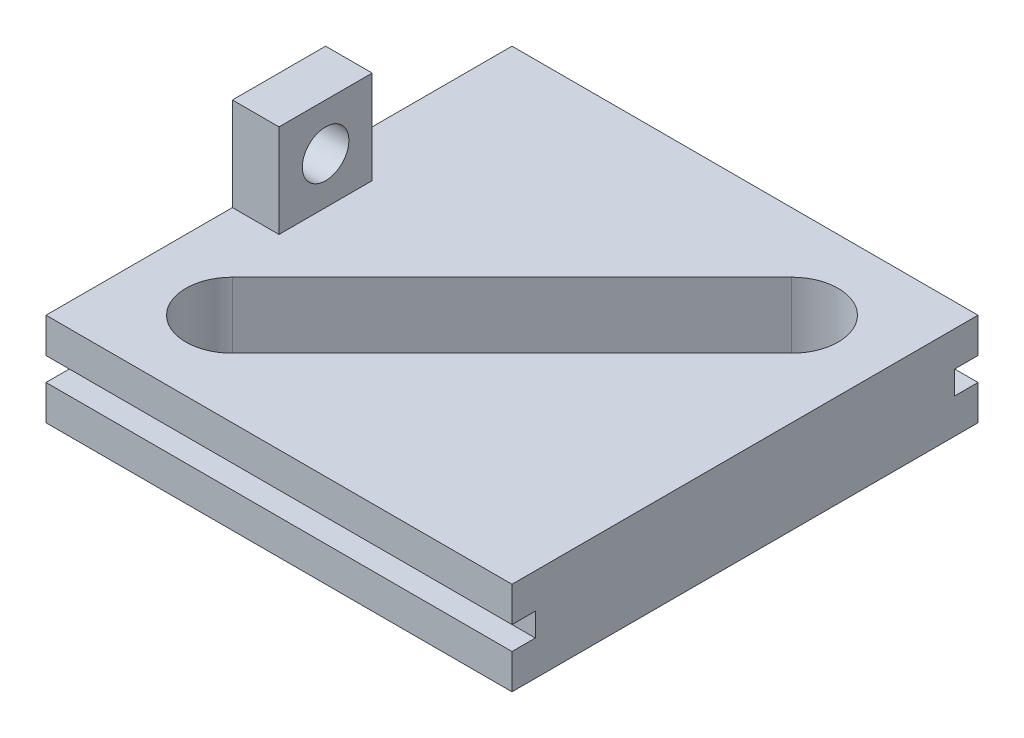
SolidWorks part; units mm, degrees
ref_plane "Front Plane" through (0, 0, 0) normal (0, 0, 1) x (1, 0, 0)
ref_plane "Top Plane" through (0, 0, 0) normal (0, 1, 0) x (1, 0, 0)
ref_plane "Right Plane" through (0, 0, 0) normal (1, 0, 0) x (0, 0, -1)
sketch "Sketch1" plane through (0, 0, 0) normal (0, 1, 0) x (1, 0, 0)
  line L0 (-23.5401, -14.5599) -> (14.5599, 23.5401)
  line L1 (31.75, 31.75) -> (-31.75, 31.75)
  line L2 (31.75, 31.75) -> (31.75, -31.75)
  line L3 (31.75, -31.75) -> (-31.75, -31.75)
  line L4 (-31.75, 31.75) -> (-31.75, -31.75)
  line L5 (31.75, 31.75) -> (-31.75, -31.75) construction
  line L6 (31.75, -31.75) -> (-31.75, 31.75) construction
  line L7 (-14.5599, -23.5401) -> (23.5401, 14.5599)
  line L8 (2.9653, 11.9455) -> (11.9455, 2.9653) construction
  line L9 (14.5599, 23.5401) -> (23.5401, 14.5599) construction
  line L10 (-19.05, -19.05) -> (19.05, 19.05) construction
  arc A0 (-23.5401, -14.5599) -> (-14.5599, -23.5401) centre (-19.05, -19.05) ccw
  arc A1 (14.5599, 23.5401) -> (23.5401, 14.5599) centre (19.05, 19.05) cw
  point P0 (0, 0)
  point P14 (7.4554, 7.4554)
  point P15 (0, 0)
  dimension "D1" = 63.5
  dimension "D2" = 38.1
  dimension "D3" = 12.7
extrude "Boss-Extrude1" add sketch "Sketch1" along normal blind 12.7
sketch "Sketch2" plane through (0, 0, 31.75) normal (0, 0, 1) x (1, 0, 0)
  line L0 (-31.75, 12.7) -> (-31.75, 0) construction
  line L1 (-31.75, 7.9375) -> (31.75, 7.9375)
  line L2 (-31.75, 7.9375) -> (-31.75, 4.7625)
  line L3 (-31.75, 4.7625) -> (31.75, 4.7625)
  line L4 (31.75, 7.9375) -> (31.75, 4.7625)
  line L5 (31.75, 12.7) -> (31.75, 0) construction
  line L6 (13.2782, 12.7) -> (13.2782, 0) construction
  line L7 (-31.75, 12.7) -> (31.75, 12.7) construction
  line L8 (-31.75, 0) -> (31.75, 0) construction
  point P14 (31.75, 6.35)
  point P15 (13.2782, 6.35)
  dimension "D1" = 3.175
extrude "Cut-Extrude1" cut sketch "Sketch2" against normal blind 3.175
mirror "Mirror1" about plane through (0, 0, 0) normal (0, 0, 1) of "Cut-Extrude1"
sketch "Sketch3" plane through (0, 12.7, 0) normal (0, 1, 0) x (1, 0, 0)
  line L0 (-31.75, 31.75) -> (-31.75, -31.75) construction
  line L1 (-31.75, 6.35) -> (-25.4, 6.35)
  line L2 (-31.75, 6.35) -> (-31.75, -6.35)
  line L3 (-31.75, -6.35) -> (-25.4, -6.35)
  line L4 (-25.4, 6.35) -> (-25.4, -6.35)
  point P6 (-25.4, 0)
  dimension "D1" = 12.7
  dimension "D2" = 6.35
extrude "Boss-Extrude2" add sketch "Sketch3" along normal blind 12.7
sketch "Sketch4" plane through (-31.75, 0, 0) normal (-1, 0, 0) x (0, 0, 1)
  line L0 (0.3824, 25.4) -> (0.3824, 12.7) construction
  line L1 (-6.35, 25.4) -> (6.35, 25.4) construction
  line L2 (6.35, 12.7) -> (31.75, 12.7) construction
  circle A0 centre (0, 19.05) radius 3.175
  point P6 (0, 0)
  point P9 (0.3824, 19.05)
  point P10 (0, 0)
  dimension "D1" = 6.35
extrude "Cut-Extrude2" cut sketch "Sketch4" against normal through all
